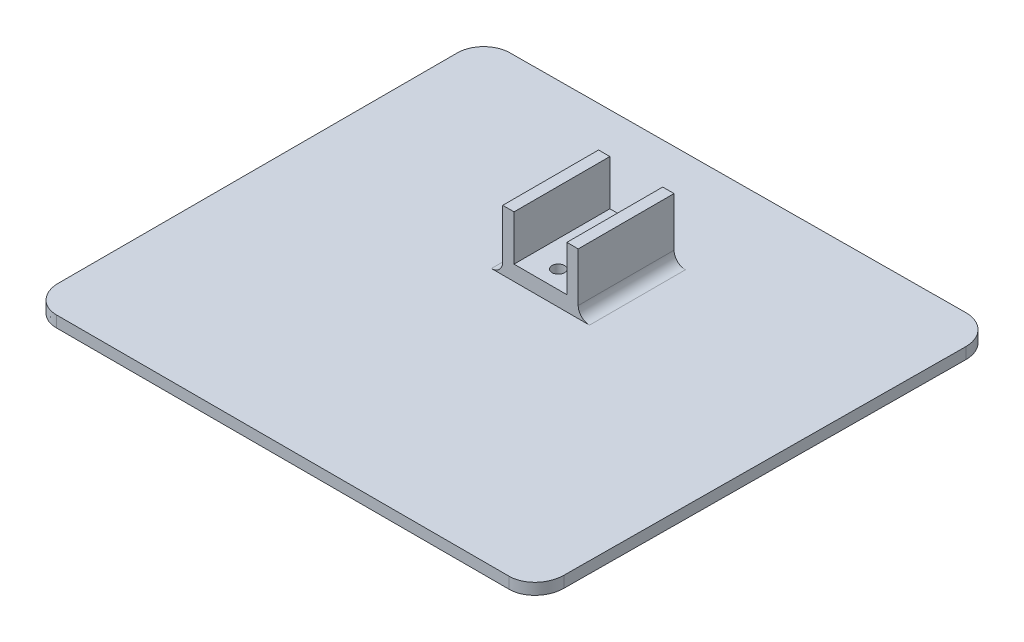
SolidWorks part; units mm, degrees
ref_plane "Front Plane" through (0, 0, 0) normal (0, 0, 1) x (1, 0, 0)
ref_plane "Top Plane" through (0, 0, 0) normal (0, 1, 0) x (1, 0, 0)
ref_plane "Right Plane" through (0, 0, 0) normal (1, 0, 0) x (0, 0, -1)
sketch "Sketch1" plane through (0, 0, 0) normal (0, 1, 0) x (1, 0, 0)
  line L5 (-5.8237, 26.114) -> (4.2283, 26.114) construction
  line L6 (-5.8237, 26.114) -> (-5.8237, 8.114) construction
  line L7 (-5.8237, 8.114) -> (4.2283, 8.114) construction
  line L8 (4.2283, 26.114) -> (4.2283, 8.114) construction
  line L12 (-67.6237, 48.8997) -> (-67.6237, -56.8014)
  line L13 (-60.6237, -64.3249) -> (59.3763, -64.3249)
  line L14 (66.3763, -56.8014) -> (67.1646, 48.8997)
  line L15 (59.3738, 56.6879) -> (-60.6237, 55.8997)
  circle A0 centre (-0.6237, 23.2931) radius 1.6559
  circle A1 centre (-0.6237, 8.6777) radius 1.6559
  arc A6 (67.1646, 48.8997) -> (59.3738, 56.6879) centre (59.3763, 48.8997) ccw
  arc A7 (-60.6237, 55.8997) -> (-67.6237, 48.8997) centre (-60.6237, 48.8997) ccw
  spline S4 degree 3 poles (-67.6237, -56.8014) (-67.6237, -57.5765) (-67.4089, -59.1032) (-66.5399, -61.0079) (-65.3341, -62.4385) (-64.1202, -63.3946) (-62.5468, -64.1272) (-61.2506, -64.3249) (-60.6237, -64.3249) knots 0 0 0 0 0.25 0.5 0.625 0.75 0.875 1 1 1 1
  spline S5 degree 3 poles (59.3763, -64.3249) (59.997, -64.3249) (61.2753, -64.1334) (62.8568, -63.4056) (64.0776, -62.4473) (65.2824, -61.0235) (66.1584, -59.1189) (66.3763, -57.581) (66.3763, -56.8014) knots 0 0 0 0 0.125 0.25 0.375 0.5 0.75 1 1 1 1
  point P18 (0, 0)
  point P19 (0, 0)
  point P20 (4.5723, 38.1009)
  point P23 (-62.0353, 78.9484)
  dimension "D1" = 18
  dimension "D2" = 60
  dimension "D3" = 59.9974
  dimension "D4" = 120
  dimension "D5" = 120
  dimension "D6" = 60
  dimension "D7" = 60
  dimension "D8" = 5.2
  dimension "D9" = 10.0519
  dimension "D10" = 14.6154
  dimension "D11" = 33
extrude "Boss-Extrude1" add sketch "Sketch1" along normal blind 3
sketch "Sketch2" plane through (0, 3, 0) normal (0, 1, 0) x (1, 0, 0)
  line L1 (-10.6237, 29.3484) -> (9.3763, 29.3484)
  line L2 (-10.6237, 29.3484) -> (-10.6237, 3.9488)
  line L3 (-10.6237, 3.9488) -> (9.3763, 3.9488)
  line L4 (9.3763, 29.3484) -> (9.3763, 3.9488)
  circle A0 centre (-0.6237, 23.2931) radius 1.6559 construction
  circle A1 centre (-0.6237, 8.6777) radius 1.6559 construction
  circle A2 centre (-0.6237, 8.6777) radius 1.6559
  circle A3 centre (-0.6237, 23.2931) radius 1.6559
  dimension "D1" = 20
  dimension "D2" = 10
extrude "Boss-Extrude2" add sketch "Sketch2" along normal blind 16
sketch "Sketch3" plane through (0, 19, 0) normal (0, 1, 0) x (1, 0, 0)
  line L1 (-7.6237, 31.8785) -> (6.3763, 31.8785)
  line L2 (-7.6237, 31.8785) -> (-7.6237, 1.4449)
  line L3 (-7.6237, 1.4449) -> (6.3763, 1.4449)
  line L4 (6.3763, 31.8785) -> (6.3763, 1.4449)
  dimension "D1" = 14
  dimension "D2" = 3
extrude "Cut-Extrude1" cut sketch "Sketch3" against normal blind 12 contours L2 L1 L4 L3
fillet "Fillet1" radius 3 2 edges at (9.3763, 3, -16.6486) (-10.6237, 3, -16.6486)
sketch "Sketch4" plane through (0, 0, 0) normal (0, -1, 0) x (1, 0, 0)
  circle A11 centre (-0.6237, -8.6777) radius 3.6559
  circle A12 centre (-0.6237, -8.6777) radius 3.6559
  circle A14 centre (-0.6237, -23.2931) radius 3.6559
  circle A15 centre (-0.6237, -23.2931) radius 3.6559
  dimension "D1" = 2
  dimension "D2" = 2
extrude "Cut-Extrude2" cut sketch "Sketch4" against normal blind 3
